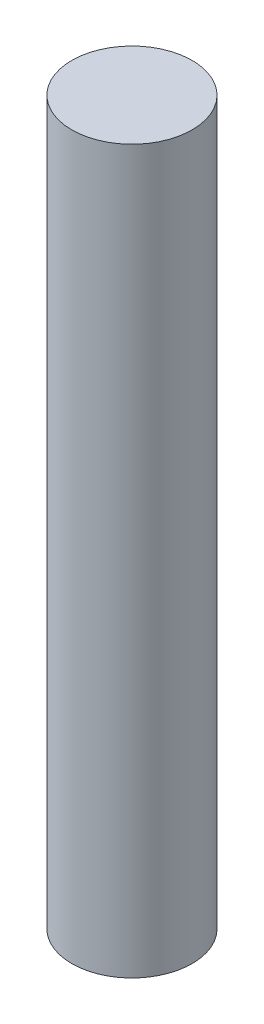
SolidWorks part; units mm, degrees
ref_plane "Front Plane" through (0, 0, 0) normal (0, 0, 1) x (1, 0, 0)
ref_plane "Top Plane" through (0, 0, 0) normal (0, 1, 0) x (1, 0, 0)
ref_plane "Right Plane" through (0, 0, 0) normal (1, 0, 0) x (0, 0, -1)
sketch "Sketch1" plane through (0, 0, 0) normal (0, 1, 0) x (1, 0, 0)
  circle A0 centre (0, 0) radius 6.35
  dimension "D1" = 12.7
extrude "Boss-Extrude1" add sketch "Sketch1" along normal blind 76.2
